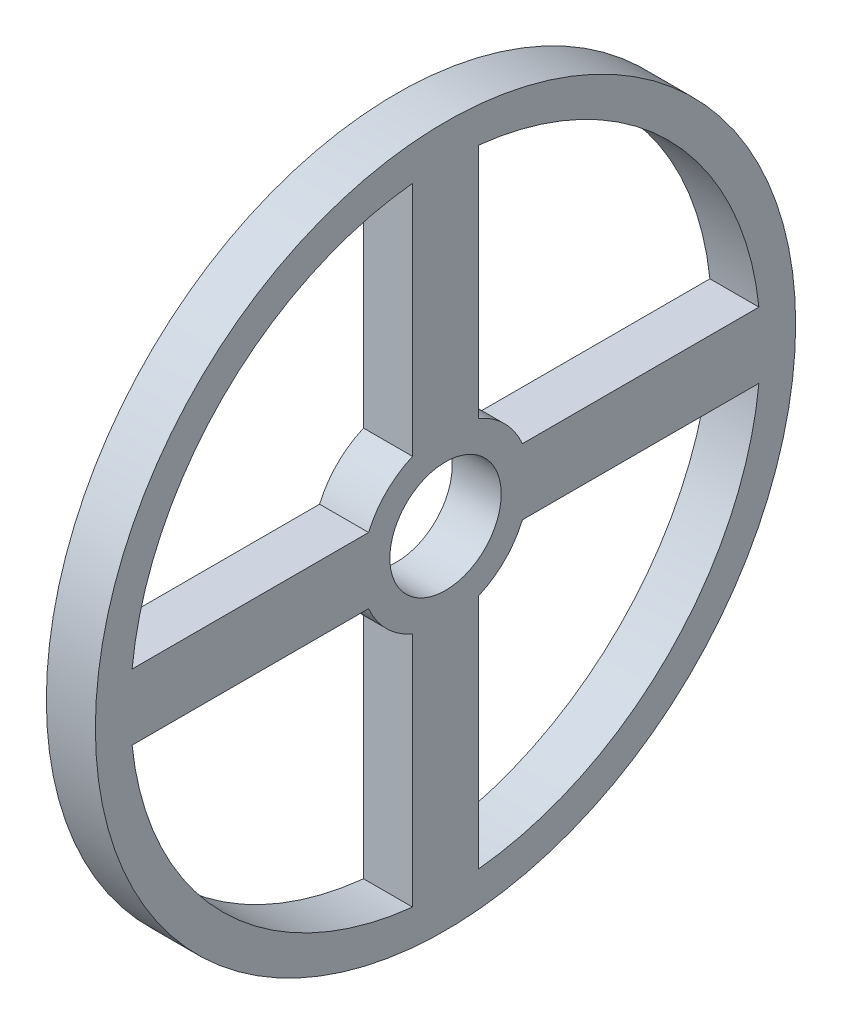
SolidWorks part; units mm, degrees
ref_plane "Front Plane" through (0, 0, 0) normal (0, 0, 1) x (1, 0, 0)
ref_plane "Top Plane" through (0, 0, 0) normal (0, 1, 0) x (1, 0, 0)
ref_plane "Right Plane" through (0, 0, 0) normal (1, 0, 0) x (0, 0, -1)
sketch "Sketch3" plane through (0, 0, 0) normal (1, 0, 0) x (0, 0, -1)
  line L0 (0, -1100) -> (0, -50) construction
  line L1 (-114.5632, -1089.996) -> (-5.2264, -49.7261) construction
  line L2 (114.5632, -1089.996) -> (5.2264, -49.7261) construction
  line L3 (0, 7.95) -> (-0.6219, 5.9174)
  line L4 (0, 7.95) -> (0.6219, 5.9174)
  line L5 (1.6529, 7.7763) -> (0.6219, 5.9174)
  line L6 (1.6529, 7.7763) -> (1.8387, 5.6588)
  line L7 (3.2336, 7.2627) -> (1.8387, 5.6588)
  line L8 (3.2336, 7.2627) -> (2.975, 5.1529)
  line L9 (4.6729, 6.4317) -> (2.975, 5.1529)
  line L10 (4.6729, 6.4317) -> (3.9813, 4.4217)
  line L11 (5.908, 5.3196) -> (3.9813, 4.4217)
  line L12 (5.908, 5.3196) -> (4.8137, 3.4973)
  line L13 (6.8849, 3.975) -> (4.8137, 3.4973)
  line L14 (6.8849, 3.975) -> (5.4356, 2.4201)
  line L15 (7.5609, 2.4567) -> (5.4356, 2.4201)
  line L16 (7.5609, 2.4567) -> (5.82, 1.2371)
  line L17 (7.9064, 0.831) -> (5.82, 1.2371)
  line L18 (7.9064, 0.831) -> (5.95, 0)
  line L19 (7.9064, -0.831) -> (5.95, 0)
  line L20 (7.9064, -0.831) -> (5.82, -1.2371)
  line L21 (7.5609, -2.4567) -> (5.82, -1.2371)
  line L22 (7.5609, -2.4567) -> (5.4356, -2.4201)
  line L23 (6.8849, -3.975) -> (5.4356, -2.4201)
  line L24 (6.8849, -3.975) -> (4.8137, -3.4973)
  line L25 (5.908, -5.3196) -> (4.8137, -3.4973)
  line L26 (5.908, -5.3196) -> (3.9813, -4.4217)
  line L27 (4.6729, -6.4317) -> (3.9813, -4.4217)
  line L28 (4.6729, -6.4317) -> (2.975, -5.1529)
  line L29 (3.2336, -7.2627) -> (2.975, -5.1529)
  line L30 (3.2336, -7.2627) -> (1.8387, -5.6588)
  line L31 (1.6529, -7.7763) -> (1.8387, -5.6588)
  line L32 (1.6529, -7.7763) -> (0.6219, -5.9174)
  line L33 (0, -7.95) -> (0.6219, -5.9174)
  line L34 (0, -7.95) -> (-0.6219, -5.9174)
  line L35 (-1.6529, -7.7763) -> (-0.6219, -5.9174)
  line L36 (-1.6529, -7.7763) -> (-1.8387, -5.6588)
  line L37 (-3.2336, -7.2627) -> (-1.8387, -5.6588)
  line L38 (-3.2336, -7.2627) -> (-2.975, -5.1529)
  line L39 (-4.6729, -6.4317) -> (-2.975, -5.1529)
  line L40 (-4.6729, -6.4317) -> (-3.9813, -4.4217)
  line L41 (-5.908, -5.3196) -> (-3.9813, -4.4217)
  line L42 (-5.908, -5.3196) -> (-4.8137, -3.4973)
  line L43 (-6.8849, -3.975) -> (-4.8137, -3.4973)
  line L44 (-6.8849, -3.975) -> (-5.4356, -2.4201)
  line L45 (-7.5609, -2.4567) -> (-5.4356, -2.4201)
  line L46 (-7.5609, -2.4567) -> (-5.82, -1.2371)
  line L47 (-7.9064, -0.831) -> (-5.82, -1.2371)
  line L48 (-7.9064, -0.831) -> (-5.95, 0)
  line L49 (-7.9064, 0.831) -> (-5.95, 0)
  line L50 (-7.9064, 0.831) -> (-5.82, 1.2371)
  line L51 (-7.5609, 2.4567) -> (-5.82, 1.2371)
  line L52 (-7.5609, 2.4567) -> (-5.4356, 2.4201)
  line L53 (-6.8849, 3.975) -> (-5.4356, 2.4201)
  line L54 (-6.8849, 3.975) -> (-4.8137, 3.4973)
  line L55 (-5.908, 5.3196) -> (-4.8137, 3.4973)
  line L56 (-5.908, 5.3196) -> (-3.9813, 4.4217)
  line L57 (-4.6729, 6.4317) -> (-3.9813, 4.4217)
  line L58 (-4.6729, 6.4317) -> (-2.975, 5.1529)
  line L59 (-3.2336, 7.2627) -> (-2.975, 5.1529)
  line L60 (-3.2336, 7.2627) -> (-1.8387, 5.6588)
  line L61 (-1.6529, 7.7763) -> (-1.8387, 5.6588)
  line L62 (-1.6529, 7.7763) -> (-0.6219, 5.9174)
  line L71 (-4.7038, -44.7535) -> (0.831, 7.9064) construction
  line L72 (0, -7.95) -> (0, 7.758) construction
  line L73 (4.7038, -44.7535) -> (-0.831, 7.9064) construction
  line L74 (-4.7089, 44.753) -> (-4.7089, 10.9831)
  line L75 (4.7089, 44.753) -> (4.7089, 10.9831)
  line L76 (44.753, -4.7089) -> (10.9831, -4.7089)
  line L77 (44.753, 4.7089) -> (10.9831, 4.7089)
  line L78 (-4.7089, -44.753) -> (-4.7089, -10.9831)
  line L79 (4.7089, -44.753) -> (4.7089, -10.9831)
  line L80 (-44.753, 4.7089) -> (-10.9831, 4.7089)
  line L81 (-44.753, -4.7089) -> (-10.9831, -4.7089)
  circle A0 centre (0, 0) radius 7.95
  arc A1 (-4.7089, 10.9831) -> (-10.9831, 4.7089) centre (0, 0) ccw
  circle A2 centre (0, 0) radius 50
  circle A4 centre (0, 0) radius 5.95 construction
  arc A5 (44.753, 4.7089) -> (4.7038, 44.7535) centre (0, 0) ccw
  circle A6 centre (0, 0) radius 11.95 construction
  arc A7 (10.9831, 4.7089) -> (4.7089, 10.9831) centre (0, 0) ccw
  arc A10 (-10.9831, -4.7089) -> (-4.7089, -10.9831) centre (0, 0) ccw
  arc A12 (4.7089, -10.9831) -> (10.9831, -4.7089) centre (0, 0) ccw
  arc A13 (-4.7038, 44.7535) -> (-44.753, 4.7089) centre (0, 0) ccw
  arc A14 (-44.753, -4.7089) -> (-4.7038, -44.7535) centre (0, 0) ccw
  arc A15 (4.7038, -44.7535) -> (44.753, -4.7089) centre (0, 0) ccw
  point P79 (0, 0)
  point P105 (0, 0)
  point P117 (0, 0)
  dimension "D1" = 15.9
  dimension "D3" = 100
  dimension "D8" = 90
  dimension "D4" = 6
  dimension "D5" = 2
  dimension "D2" = 4
  dimension "D6" = 30
  dimension "D7" = 4
extrude "Boss-Extrude3" add sketch "Sketch3" along normal blind 7
